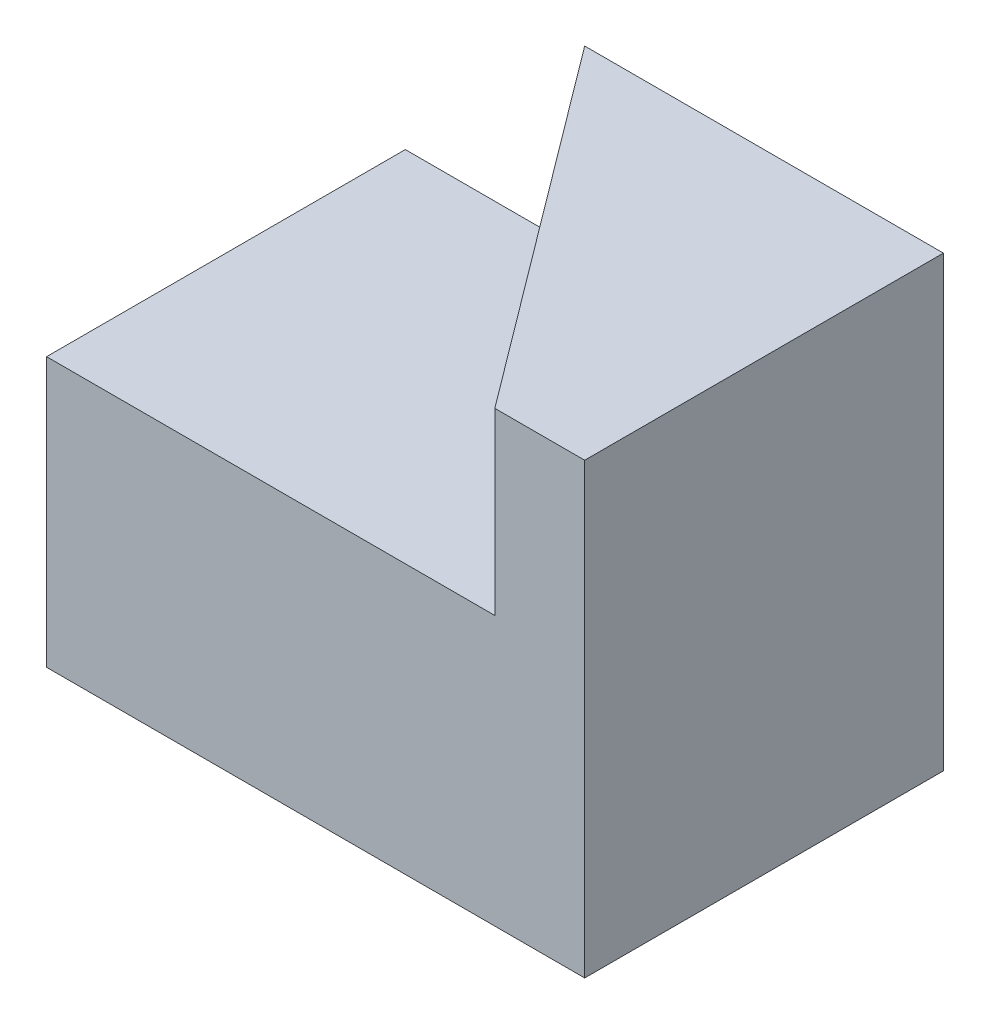
SolidWorks part; units mm, degrees
ref_plane "Front Plane" through (0, 0, 0) normal (0, 0, 1) x (1, 0, 0)
ref_plane "Top Plane" through (0, 0, 0) normal (0, 1, 0) x (1, 0, 0)
ref_plane "Right Plane" through (0, 0, 0) normal (1, 0, 0) x (0, 0, -1)
sketch "Sketch1" plane through (0, 0, 0) normal (0, 1, 0) x (1, 0, 0)
  line L1 (0, 0) -> (6, 0)
  line L2 (0, 0) -> (0, 4)
  line L3 (0, 4) -> (6, 4)
  line L4 (6, 0) -> (6, 4)
  dimension "D1" = 6
  dimension "D2" = 4
extrude "Boss-Extrude1" add sketch "Sketch1" along normal blind 3
sketch "Sketch3" plane through (0, 3, 0) normal (0, 1, 0) x (1, 0, 0)
  line L0 (6, 4) -> (6, 0)
  line L1 (6, 0) -> (4.9979, 0)
  line L2 (0, 0) -> (6, 0) construction
  line L3 (4.9979, 0) -> (2, 4)
  line L4 (6, 4) -> (0, 4) construction
  line L5 (2, 4) -> (6, 4)
  dimension "D1" = 4
extrude "Boss-Extrude2" add sketch "Sketch3" along normal blind 2
